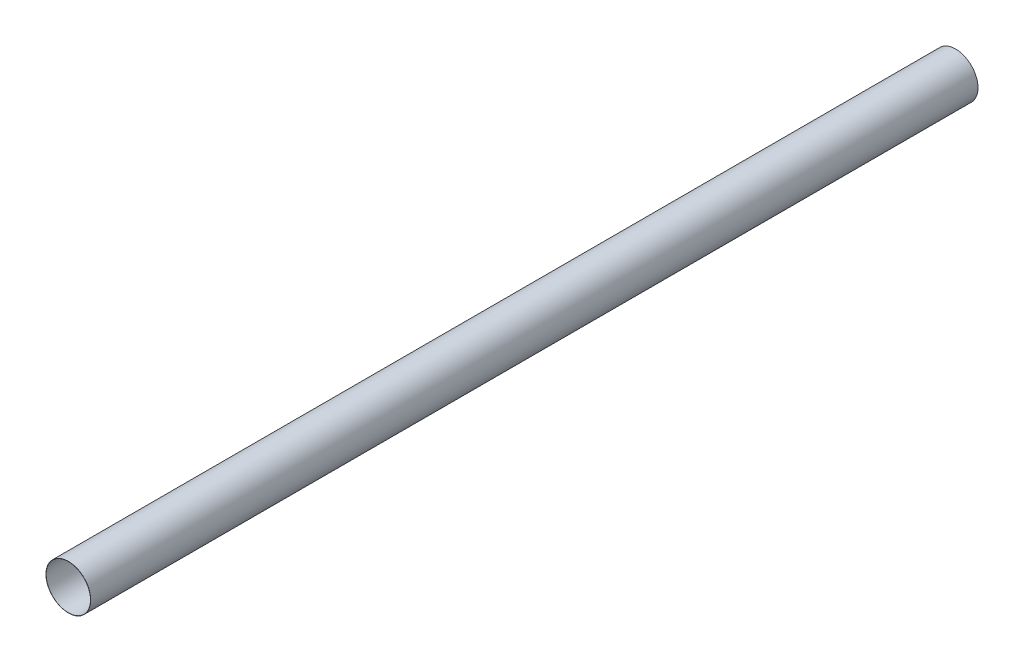
SolidWorks part; units mm, degrees
material "Gray Cast Iron"
ref_plane "Front Plane" through (0, 0, 0) normal (0, 0, 1) x (1, 0, 0)
ref_plane "Top Plane" through (0, 0, 0) normal (0, 1, 0) x (1, 0, 0)
ref_plane "Right Plane" through (0, 0, 0) normal (1, 0, 0) x (0, 0, -1)
sketch "Sketch1" plane through (0, 0, 0) normal (0, 0, 1) x (1, 0, 0)
  circle A0 centre (0, 0) radius 252
  circle A1 centre (0, 0) radius 250
extrude "Boss-Extrude1" add sketch "Sketch1" along normal blind 10000
